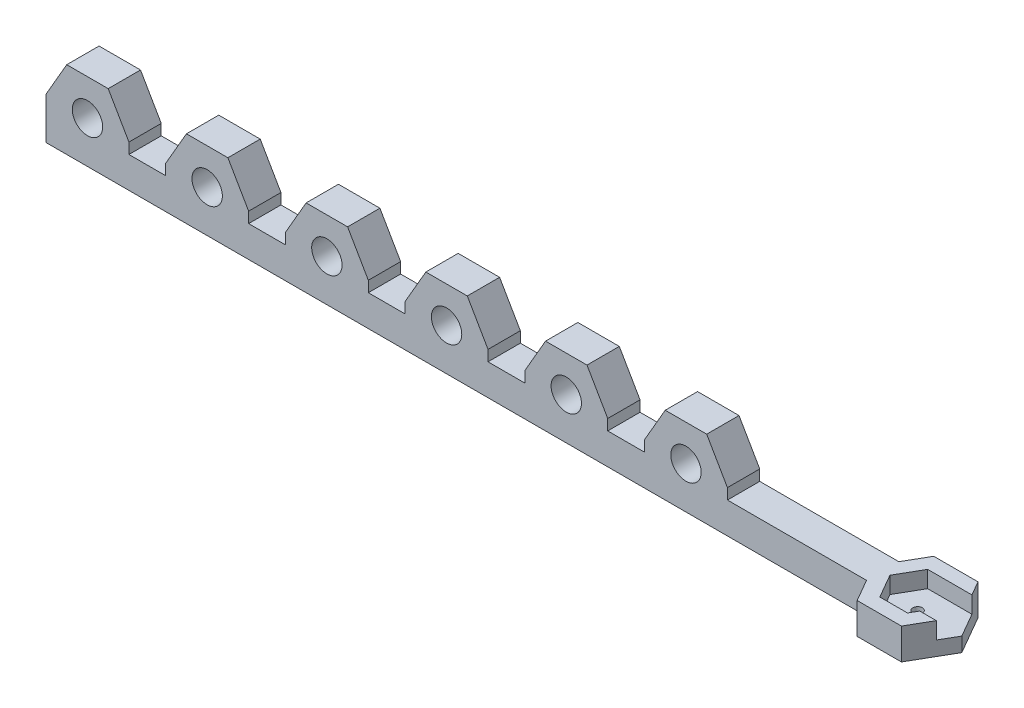
SolidWorks part; units mm, degrees
ref_plane "Front Plane" through (0, 0, 0) normal (0, 0, 1) x (1, 0, 0)
ref_plane "Top Plane" through (0, 0, 0) normal (0, 1, 0) x (1, 0, 0)
ref_plane "Right Plane" through (0, 0, 0) normal (1, 0, 0) x (0, 0, -1)
sketch "Sketch1" plane through (0, 0, 0) normal (0, 1, 0) x (1, 0, 0)
  line L1 (0, 0) -> (175, 0)
  line L2 (0, 0) -> (0, -6.75)
  line L3 (0, -6.75) -> (175, -6.75)
  line L4 (175, 0) -> (175, -6.75)
  dimension "D1" = 6.75
  dimension "D2" = 175
extrude "Boss-Extrude1" add sketch "Sketch1" along normal blind 6.5
sketch "Sketch2" plane through (0, 6.5, 0) normal (0, 1, 0) x (1, 0, 0)
  line L0 (175, 0) -> (0, 0) construction
  line L1 (0, 0) -> (10, 0)
  line L2 (0, 0) -> (0, -6.75)
  line L3 (0, -6.75) -> (10, -6.75)
  line L4 (10, 0) -> (10, -6.75)
  line L5 (0, -6.75) -> (175, -6.75) construction
  line L6 (0, 0) -> (0, -6.75) construction
  dimension "D1" = 10
extrude "Boss-Extrude2" add sketch "Sketch2" along normal blind 7.5
sketch "Sketch5" plane through (0, 0, 6.75) normal (0, 0, 1) x (1, 0, 0)
  line L1 (10, 14) -> (10, 6.5) construction
  circle A0 centre (5, 8.75) radius 3.175
  dimension "D3" = 6.35
  dimension "D1" = 8.75
  dimension "D2" = 5
extrude "Cut-Extrude2" cut sketch "Sketch5" against normal blind 10
ref_plane "Plane1" through (0, 0, 3.375) normal (0, 0, 1) x (1, 0, 0)
pattern_linear "LPattern1" count 6 spacing 25 along (1, 0, 0) of "Cut-Extrude2", "Boss-Extrude2"
sketch "Sketch6" plane through (0, 0, 6.75) normal (0, 0, 1) x (1, 0, 0)
  line L0 (138.6603, 8.75) -> (138.6603, 0)
  line L1 (138.6603, 8.75) -> (134.3301, 16.25)
  line L2 (134.3301, 16.25) -> (125.6699, 16.25)
  line L3 (125.6699, 16.25) -> (121.3397, 8.75)
  line L4 (121.3397, 8.75) -> (125.6699, 1.25) construction
  line L5 (125.6699, 1.25) -> (134.3301, 1.25) construction
  line L6 (134.3301, 1.25) -> (138.6603, 8.75) construction
  line L7 (0, 0) -> (175, 0) construction
  line L8 (121.3397, 8.75) -> (121.3397, 0)
  line L9 (121.3397, 0) -> (138.6603, 0)
  circle A0 centre (130, 8.75) radius 7.5 construction
  circle A1 centre (130, 8.75) radius 3.175
  circle A2 centre (130, 8.75) radius 3.175 construction
  dimension "D1" = 7.5
extrude "Boss-Extrude4" add sketch "Sketch6" against normal up to surface (6.75 mm away) up to face at (33.175, 8.75, 0)
pattern_linear "LPattern2" count 6 spacing 25 along (-1, 0, 0) of "Boss-Extrude4"
sketch "Sketch7" plane through (0, 6.5, 0) normal (0, 1, 0) x (1, 0, 0)
  line L0 (175, -6.75) -> (175, 0) construction
  line L1 (172.1132, -8.375) -> (177.8868, -8.375)
  line L2 (177.8868, -8.375) -> (180.7735, -3.375) construction
  line L3 (180.7735, -3.375) -> (177.8868, 1.625) construction
  line L4 (177.8868, 1.625) -> (172.1132, 1.625)
  line L5 (172.1132, 1.625) -> (169.2265, -3.375)
  line L6 (169.2265, -3.375) -> (172.1132, -8.375)
  line L7 (138.6603, -6.75) -> (175, -6.75) construction
  line L8 (179.6188, -11.375) -> (182.289, -6.75)
  line L9 (170.3812, -11.375) -> (179.6188, -11.375)
  line L10 (179.6188, -11.375) -> (184.2376, -3.375) construction
  line L11 (184.2376, -3.375) -> (179.6188, 4.625) construction
  line L12 (179.6188, 4.625) -> (170.3812, 4.625)
  line L13 (170.3812, 4.625) -> (165.7624, -3.375)
  line L14 (165.7624, -3.375) -> (170.3812, -11.375)
  line L15 (175, -6.75) -> (182.289, -6.75) construction
  line L16 (177.8868, -8.375) -> (178.8249, -6.75)
  line L17 (178.8249, -6.75) -> (182.289, -6.75)
  line L18 (177.8868, 1.625) -> (181.3509, 1.625)
  line L19 (181.3509, 1.625) -> (179.6188, 4.625)
  circle A0 centre (175, -3.375) radius 5 construction
  circle A1 centre (175, -3.375) radius 8 construction
  dimension "D1" = 5
  dimension "D2" = 8
extrude "Boss-Extrude5" add sketch "Sketch7" against normal blind 6.5
sketch "Sketch9" plane through (0, 0, 0) normal (0, -1, 0) x (-1, 0, 0)
  line L0 (-171.1751, 0) -> (-172.1132, 1.625) construction
  line L1 (-169.2265, -3.375) -> (-172.1132, 1.625)
  line L2 (-172.1132, 1.625) -> (-177.8868, 1.625)
  line L3 (-177.8868, 1.625) -> (-180.7735, -3.375) construction
  line L4 (-180.7735, -3.375) -> (-177.8868, -8.375) construction
  line L5 (-177.8868, -8.375) -> (-172.1132, -8.375)
  line L6 (-172.1132, -8.375) -> (-169.2265, -3.375)
  line L7 (-172.1132, -8.375) -> (-171.1751, -6.75) construction
  line L8 (-178.8249, -6.75) -> (-182.289, -6.75)
  line L9 (-182.289, -6.75) -> (-184.2376, -3.375)
  line L10 (-184.2376, -3.375) -> (-181.3509, 1.625)
  line L11 (-181.3509, 1.625) -> (-179.6188, 4.625) construction
  line L12 (-179.6188, -11.375) -> (-182.289, -6.75) construction
  line L13 (-177.8868, 1.625) -> (-181.3509, 1.625)
  line L14 (-178.8249, -6.75) -> (-177.8868, -8.375)
  circle A0 centre (-175, -3.375) radius 5 construction
extrude "Boss-Extrude6" add sketch "Sketch9" against normal blind 3
sketch "Sketch10" plane through (0, 0, 0) normal (0, -1, 0) x (-1, 0, 0)
  line L0 (-175, -11.375) -> (-175, 4.625) construction
  line L1 (-170.3812, -11.375) -> (-179.6188, -11.375) construction
  line L2 (-179.6188, 4.625) -> (-170.3812, 4.625) construction
  circle A1 centre (-175, -3.375) radius 2.575
  point P0 (-175, -3.375)
  dimension "D1" = 5.15
extrude "Cut-Extrude4" cut sketch "Sketch10" against normal blind 2
sketch "Sketch11" plane through (0, 3, 0) normal (0, 1, 0) x (1, 0, 0)
  line L0 (177.8868, -8.375) -> (172.1132, -8.375) construction
  line L1 (180.7735, -3.375) -> (177.8868, 1.625)
  line L2 (177.8868, 1.625) -> (172.1132, 1.625)
  line L3 (172.1132, 1.625) -> (169.2265, -3.375)
  line L4 (169.2265, -3.375) -> (172.1132, -8.375)
  line L5 (172.1132, -8.375) -> (177.8868, -8.375)
  line L6 (177.8868, -8.375) -> (180.7735, -3.375)
  line L7 (171.1751, 0) -> (172.1132, 1.625) construction
  circle A0 centre (175, -3.375) radius 5 construction
extrude "Cut-Extrude5" cut sketch "Sketch11" along normal blind 18
sketch "Sketch12" plane through (0, 3, 0) normal (0, 1, 0) x (1, 0, 0)
  circle A0 centre (175, -3.375) radius 1
  dimension "D1" = 2
extrude "Cut-Extrude6" cut sketch "Sketch12" against normal blind 10 contours A0
